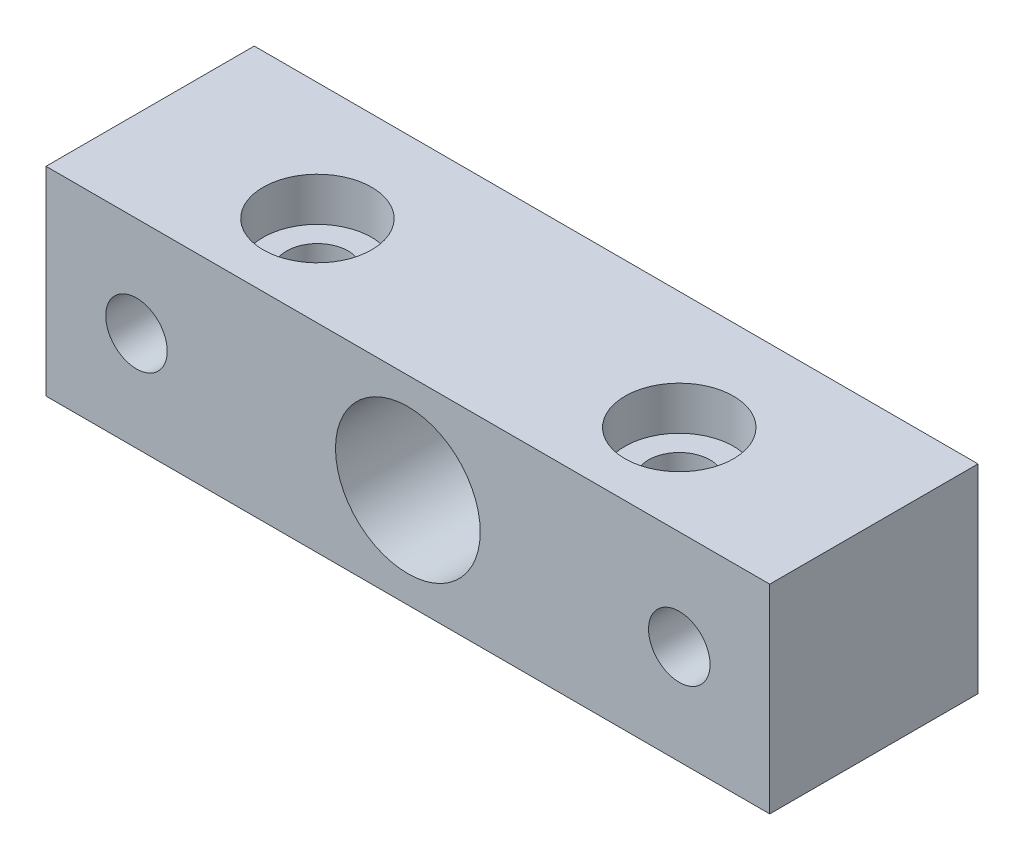
SolidWorks part; units mm, degrees
ref_plane "Plan de face" through (0, 0, 0) normal (0, 0, 1) x (1, 0, 0)
ref_plane "Plan de dessus" through (0, 0, 0) normal (0, 1, 0) x (1, 0, 0)
ref_plane "Plan de droite" through (0, 0, 0) normal (1, 0, 0) x (0, 0, -1)
sketch "Esquisse1" plane through (0, 0, 0) normal (0, 0, 1) x (1, 0, 0)
  line L0 (-2.625, 3.0182) -> (-2.625, -3.0182) construction
  line L1 (2.625, 3.0182) -> (-2.625, 3.0182) construction
  line L2 (2.625, 3.0182) -> (2.625, -3.0182) construction
  line L3 (2.625, -3.0182) -> (-2.625, -3.0182) construction
  line L5 (2.625, 3.0182) -> (-2.625, -3.0182) construction
  line L6 (2.625, -3.0182) -> (-2.625, 3.0182) construction
  line L8 (-4.341, -1.1938) -> (-20, -5.5) construction
  line L9 (20, -5.5) -> (-20, -5.5)
  line L10 (20, -5.5) -> (20, 5.5)
  line L11 (20, 5.5) -> (-20, 5.5)
  line L12 (-20, -5.5) -> (-20, 5.5)
  line L13 (20, -5.5) -> (-20, 5.5) construction
  line L14 (20, 5.5) -> (0, 0) construction
  circle A0 centre (0, 0) radius 4
  point P0 (0, 0)
  point P12 (0, 0)
  dimension "D2" = 8
  dimension "D1" = 5.25
  dimension "D5" = 40
  dimension "D6" = 11
extrude "Boss.-Extru.1" add sketch "Esquisse1" along normal blind 10.51
hole_wizard "Chambrage pour vis à tête ronde bombée M31" positions "Esquisse3D3" profile "Esquisse4" counterbore size "M3" standard "Ansi Metric"
sketch3d "Esquisse3D3"
  line L0 (15, 5.5, 9.51) -> (15, 5.5, 0) construction
  line L1 (15, 5.5, 9.51) -> (-15, 5.5, 9.51) construction
  line L2 (-15, 5.5, 9.51) -> (-15, 5.5, 0) construction
  point P0 (10, 5.5, 7.01)
  point P2 (-10, 5.5, 7.01)
  dimension "D1" = 5
  dimension "D2" = 2.5
  dimension "D3" = 2.5
  dimension "D4" = 5
sketch "Esquisse4" plane through (10, 5.5, 7.01) normal (1, 0, 0) x (0, 0, 1)
  line L0 (0, 0) -> (0, 11)
  line L1 (0, 11) -> (1.7, 11)
  line L3 (1.7, 11) -> (1.7, 2.4)
  line L4 (1.7, 2.4) -> (3.5, 2.4)
  line L5 (3.5, 2.4) -> (3.5, 0)
  line L7 (3.5, 0) -> (0, 0)
  line L11 (0, -6.35) -> (0, 107.95) construction
  dimension "Diamètre du perçage jusqu'au prochain" = 3.4
  dimension "Profondeur du perçage jusqu'au prochain" = 11
  dimension "Diamètre du chambrage" = 7
  dimension "Profondeur du chambrage" = 2.4
thread "Filetage2" pitch 0.45 start angle 0, offset 0, length 20, pitch 0.45, diameter 2.4
ref_plane "Plan3" through (5.3, 5.5, 4.51) normal (0, 0, 1) x (-1, 0, 0)
sketch "Profil de filetage3" plane through (5.3, 5.5, 4.51) normal (0, 0, 1) x (-1, 0, 0)
  line L0 (0, 0) -> (0, 0.45) construction
  line L1 (0, 0) -> (0.2436, 0.1406)
  line L2 (0.2436, 0.1406) -> (0.2436, 0.1969)
  line L3 (0.2436, 0.1969) -> (0, 0.3375)
  line L4 (0.2436, 0.1687) -> (0, 0.1687) construction
  line L11 (0, 0) -> (0, 0.3375)
  point P2 (0, 0)
  dimension "Pitch" = 0.45
  dimension "Profile_Angle" = 60
  dimension "Profile_Land" = 0.0562
  dimension "Profile_Height" = 0.2436
thread "Filetage3" pitch 0.45 start angle 0, offset 0, length 20, pitch 0.45, diameter 2.4
ref_plane "Plan4" through (-7.7, 5.5, 4.51) normal (0, 0, 1) x (-1, 0, 0)
sketch "Profil de filetage4" plane through (-7.7, 5.5, 4.51) normal (0, 0, 1) x (-1, 0, 0)
  line L0 (0, 0) -> (0, 0.45) construction
  line L1 (0, 0) -> (0.2436, 0.1406)
  line L2 (0.2436, 0.1406) -> (0.2436, 0.1969)
  line L3 (0.2436, 0.1969) -> (0, 0.3375)
  line L4 (0.2436, 0.1687) -> (0, 0.1687) construction
  line L11 (0, 0) -> (0, 0.3375)
  point P2 (0, 0)
  dimension "Pitch" = 0.45
  dimension "Profile_Angle" = 60
  dimension "Profile_Land" = 0.0562
  dimension "Profile_Height" = 0.2436
sketch "Esquisse16" plane through (0, 0, 10.51) normal (0, 0, 1) x (1, 0, 0)
  line L1 (-20, 5.5) -> (20, 5.5)
  line L2 (-20, 5.5) -> (-20, -5.5)
  line L3 (-20, -5.5) -> (20, -5.5)
  line L4 (20, 5.5) -> (20, -5.5)
extrude "Boss.-Extru.2" add sketch "Esquisse16" along normal blind 7
hole_wizard "Dégagement M32" positions "Esquisse17" profile "Esquisse18" hole size "M3" standard "Ansi Metric" end condition through all
sketch "Esquisse17" plane through (0, 0, 17.51) normal (0, 0, 1) x (1, 0, 0)
  point P0 (0, 0)
sketch "Esquisse18" plane through (0, 0, 17.51) normal (1, 0, 0) x (0, -1, 0)
  line L0 (0, 0) -> (0, 17.51)
  line L1 (0, 17.51) -> (1.25, 17.51)
  line L2 (1.25, 17.51) -> (1.25, 0)
  line L5 (1.25, 0) -> (0, 0)
  line L11 (0, -6.35) -> (0, 107.95) construction
  dimension "Diamètre du perçage jusqu'au prochain" = 2.5
  dimension "Profondeur du perçage jusqu'au prochain" = 17.51
sketch "Esquisse19" plane through (0, 0, 17.51) normal (0, 0, 1) x (1, 0, 0)
  line L0 (-3.5, 1.5) -> (-3.5, -1.5) construction
  line L1 (-2.5, 1.5) -> (-2.5, -1.5)
  line L2 (-4.5, 1.5) -> (-4.5, -1.5)
  line L3 (3.5, 1.5) -> (3.5, -1.5) construction
  line L4 (4.5, 1.5) -> (4.5, -1.5)
  line L5 (2.5, 1.5) -> (2.5, -1.5)
  arc A0 (-2.5, 1.5) -> (-4.5, 1.5) centre (-3.5, 1.5) ccw
  arc A1 (-4.5, -1.5) -> (-2.5, -1.5) centre (-3.5, -1.5) ccw
  arc A3 (4.5, 1.5) -> (2.5, 1.5) centre (3.5, 1.5) ccw
  arc A4 (2.5, -1.5) -> (4.5, -1.5) centre (3.5, -1.5) ccw
  circle A5 centre (0, 0) radius 1.25 construction
  point P2 (-3.5, 0)
  point P7 (3.5, 0)
  dimension "D5" = 3.5
  dimension "D3" = 3
  dimension "D6" = 3.5
  dimension "D8" = 5.5
  dimension "D1" = 1
  dimension "D2" = 1
  dimension "D4" = 3
  dimension "D7" = 5.5
extrude "Enlèv. mat.-Extru.1" [suppressed] cut sketch "Esquisse19" against normal blind 7
thread "Filetage4" pitch 0.5 start angle 0, offset 0, length 20, pitch 0.5, diameter 3.4
ref_plane "Plan5" through (-1.7, 0, 14.51) normal (0, -1, 0) x (-1, 0, 0)
sketch "Profil de filetage5" plane through (-1.7, 0, 14.51) normal (0, -1, 0) x (-1, 0, 0)
  line L0 (0, 0) -> (0, 0.5) construction
  line L1 (0, 0) -> (0.2706, 0.1562)
  line L2 (0.2706, 0.1562) -> (0.2706, 0.2187)
  line L3 (0.2706, 0.2187) -> (0, 0.375)
  line L4 (0.2706, 0.1875) -> (0, 0.1875) construction
  line L11 (0, 0) -> (0, 0.375)
  point P2 (0, 0)
  dimension "Pitch" = 0.5
  dimension "Profile_Angle" = 60
  dimension "Profile_Land" = 0.0625
  dimension "Profile_Height" = 0.2706
hole_wizard "Chambrage pour vis à tête ronde bombée M32" positions "Esquisse22" profile "Esquisse23" counterbore size "M3" standard "Ansi Metric" end condition through all
sketch "Esquisse22" plane through (0, 5.5, 0) normal (0, 1, 0) x (1, 0, 0)
  point P0 (10, -9.51)
  point P2 (-10, -9.51)
  dimension "D1" = 8
  dimension "D2" = 8
  dimension "D3" = 10
  dimension "D4" = 10
sketch "Esquisse23" plane through (10, 5.5, 9.51) normal (1, 0, 0) x (0, 0, 1)
  line L0 (0, 0) -> (0, 11)
  line L1 (0, 11) -> (1.7, 11)
  line L3 (1.7, 11) -> (1.7, 2.4)
  line L4 (1.7, 2.4) -> (3, 2.4)
  line L5 (3, 2.4) -> (3, 0)
  line L7 (3, 0) -> (0, 0)
  line L11 (0, -6.35) -> (0, 107.95) construction
  dimension "Diamètre du perçage jusqu'au prochain" = 3.4
  dimension "Profondeur du perçage jusqu'au prochain" = 11
  dimension "Diamètre du chambrage" = 6
  dimension "Profondeur du chambrage" = 2.4
sketch "Esquisse24" plane through (0, 0, 0) normal (0, 0, -1) x (-1, 0, 0)
  line L1 (20, -5.5) -> (-20, -5.5)
  line L2 (20, -5.5) -> (20, 5.5)
  line L3 (20, 5.5) -> (-20, 5.5)
  line L4 (-20, -5.5) -> (-20, 5.5)
  line L5 (20, -5.5) -> (-20, 5.5) construction
  line L6 (20, 5.5) -> (-20, -5.5) construction
  point P0 (0, 0)
extrude "Boss.-Extru.3" [suppressed] add sketch "Esquisse24" along normal blind 1
sketch "Esquisse25" [suppressed] plane through (0, 0, -1) normal (0, 0, -1) x (-1, 0, 0)
  line L0 (-2.625, 2.625) -> (-2.625, -2.625) construction
  line L1 (2.625, 2.625) -> (-2.625, 2.625) construction
  line L2 (2.625, 2.625) -> (2.625, -2.625) construction
  line L3 (2.625, -2.625) -> (-2.625, -2.625) construction
  line L4 (2.625, 2.625) -> (-2.625, -2.625) construction
  line L5 (2.625, -2.625) -> (-2.625, 2.625) construction
  line L6 (-4.227, -1.5499) -> (-14.4118, -5.2843) construction
  line L7 (14.4118, -5.2843) -> (-14.4118, -5.2843) construction
  line L8 (14.4118, -5.2843) -> (14.4118, 5.2843) construction
  line L9 (14.4118, 5.2843) -> (-14.4118, 5.2843) construction
  line L10 (-14.4118, -5.2843) -> (-14.4118, 5.2843) construction
  line L11 (14.4118, -5.2843) -> (-14.4118, 5.2843) construction
  line L12 (14.4118, 5.2843) -> (0, 0) construction
  circle A0 centre (0, 0) radius 3.7123
  point P0 (0, 0)
  point P7 (0, 0)
extrude "Enlèv. mat.-Extru.3" [suppressed] cut sketch "Esquisse25" against normal blind 3.5
hole_wizard "Fraisage pour vis à tête fraisée M31" positions "Esquisse31" profile "Esquisse32" countersink size "M3" standard "Ansi Metric"
sketch "Esquisse31" plane through (0, 0, 17.51) normal (0, 0, 1) x (1, 0, 0)
  point P0 (-15, 0)
  point P2 (15, 0)
  dimension "D1" = 5.5
  dimension "D2" = 5
  dimension "D3" = 5
  dimension "D4" = 5.5
sketch "Esquisse32" plane through (-15, 0, 17.51) normal (1, 0, 0) x (0, -1, 0)
  line L0 (0, 0) -> (0, 9.0215)
  line L1 (0, 9.0215) -> (1.7, 8)
  line L2 (1.7, 8) -> (1.7, 1.45)
  line L3 (1.7, 1.45) -> (3.15, 0)
  line L5 (3.15, 0) -> (0, 0)
  line L6 (-1.7, 1.45) -> (-3.15, 0) construction
  line L10 (0, 9.0215) -> (-1.7, 8) construction
  line L11 (0, -6.35) -> (0, 107.95) construction
  dimension "Diamètre du perçage" = 3.4
  dimension "Profondeur du perçage" = 8
  dimension "Diamètre du fraisage entrant" = 6.3
  dimension "Angle du fraisage entrant" = 90
  dimension "Angle de pointe" = 118
sketch "Esquisse33" plane through (0, 0, 17.51) normal (0, 0, 1) x (1, 0, 0)
  line L1 (50.4275, -45.0734) -> (-50.4275, -45.0734)
  line L2 (50.4275, -45.0734) -> (50.4275, 45.0734)
  line L3 (50.4275, 45.0734) -> (-50.4275, 45.0734)
  line L4 (-50.4275, -45.0734) -> (-50.4275, 45.0734)
  line L5 (50.4275, -45.0734) -> (-50.4275, 45.0734) construction
  line L6 (50.4275, 45.0734) -> (-50.4275, -45.0734) construction
  point P0 (0, 0)
extrude "Enlèv. mat.-Extru.4" cut sketch "Esquisse33" against normal blind 3
sketch "Esquisse34" plane through (0, 0, 14.51) normal (0, 0, 1) x (1, 0, 0)
  circle A0 centre (0, 0) radius 4
  dimension "D1" = 8
extrude "Enlèv. mat.-Extru.5" cut sketch "Esquisse34" against normal blind 10
sketch "Esquisse35" plane through (0, 0, 0) normal (0, 0, -1) x (-1, 0, 0)
  line L1 (39.3979, -20.4785) -> (-39.3979, -20.4785)
  line L2 (39.3979, -20.4785) -> (39.3979, 20.4785)
  line L3 (39.3979, 20.4785) -> (-39.3979, 20.4785)
  line L4 (-39.3979, -20.4785) -> (-39.3979, 20.4785)
  line L5 (39.3979, -20.4785) -> (-39.3979, 20.4785) construction
  line L6 (39.3979, 20.4785) -> (-39.3979, -20.4785) construction
  point P0 (0, 0)
extrude "Enlèv. mat.-Extru.6" cut sketch "Esquisse35" against normal blind 3
